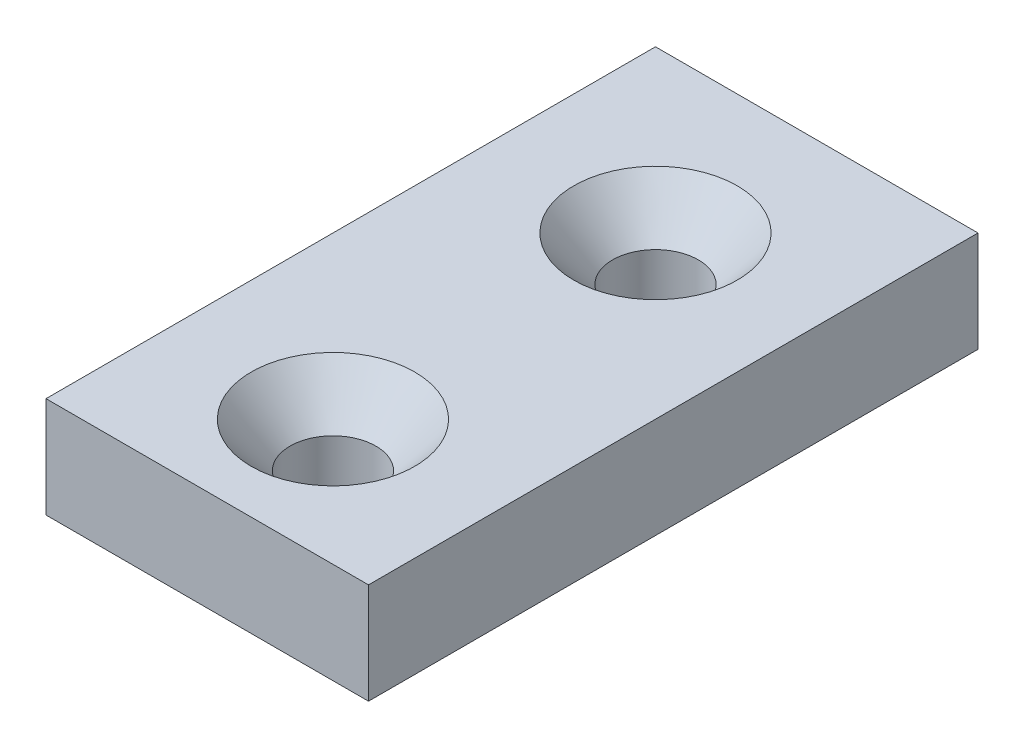
SolidWorks part; units mm, degrees
ref_plane "Front Plane" through (0, 0, 0) normal (0, 0, 1) x (1, 0, 0)
ref_plane "Top Plane" through (0, 0, 0) normal (0, 1, 0) x (1, 0, 0)
ref_plane "Right Plane" through (0, 0, 0) normal (1, 0, 0) x (0, 0, -1)
sketch "Sketch1" plane through (0, 0, 0) normal (0, 0, 1) x (1, 0, 0)
  line L0 (0, 3.9688) -> (0, -3.9688)
  line L1 (-12.7, 0) -> (12.7, 0) construction
  point P6 (0, 0)
  dimension "Width" = 25.4
  dimension "Thk" = 7.9375
sketch "Sketch2" plane through (0, 0, 0) normal (1, 0, 0) x (0, 0, -1)
  line L0 (152.4, 0) -> (-152.4, 0)
  point P4 (0, 0)
  dimension "Length" = 304.8
sketch "Sketch3" plane through (0, 0, 0) normal (0, 0, 1) x (1, 0, 0)
  line L1 (12.7, 3.9688) -> (-12.7, 3.9688)
  line L2 (12.7, 3.9688) -> (12.7, -3.9688)
  line L3 (12.7, -3.9688) -> (-12.7, -3.9688)
  line L4 (-12.7, 3.9688) -> (-12.7, -3.9688)
  line L5 (12.7, 3.9688) -> (-12.7, -3.9688) construction
  line L6 (12.7, -3.9688) -> (-12.7, 3.9688) construction
  point P0 (0, 0)
extrude "Boss-Extrude1" add sketch "Sketch3" along normal mid plane 48
sketch "Sketch5" plane through (0, 3.9688, 0) normal (0, 1, 0) x (1, 0, 0)
  line L1 (12.7, 24) -> (12.7, -24) construction
  line L3 (12.7, 24) -> (-12.7, 24) construction
  circle A0 centre (0, 11.3) radius 3.5
  circle A4 centre (0, -14.1) radius 3.5
  point P6 (4.5524, -13.8275)
  point P9 (0, -19.0302)
  point P10 (0, -15.2133)
  dimension "D1" = 7
  dimension "D2" = 12.7
  dimension "D3" = 12.7
  dimension "D4" = 25.4
hole_wizard "CSK for 1/4 Flat Head Machine Screw1" positions "Sketch6" profile "Sketch7" countersink size "1/4" standard "ANSI Inch" end condition through all
sketch "Sketch6" plane through (0, 3.9688, 0) normal (0, 1, 0) x (-1, 0, 0)
  point P0 (0, 14.1)
  point P3 (0, -11.3)
sketch "Sketch7" plane through (0, 3.9688, 14.1) normal (1, 0, 0) x (0, 0, 1)
  line L0 (0, 0) -> (0, 7.9375)
  line L1 (0, 7.9375) -> (3.3782, 7.9375)
  line L2 (3.3782, 7.9375) -> (3.3782, 3.5209)
  line L3 (3.3782, 3.5209) -> (6.4389, 0)
  line L5 (6.4389, 0) -> (0, 0)
  line L6 (-3.3782, 3.5209) -> (-6.4389, 0) construction
  line L11 (0, -6.35) -> (0, 107.95) construction
  dimension "Thru Hole Dia." = 6.7564
  dimension "Thru Hole Depth" = 7.9375
  dimension "Near C'Sink Dia." = 12.8778
  dimension "Near C'Sink Angle" = 82
